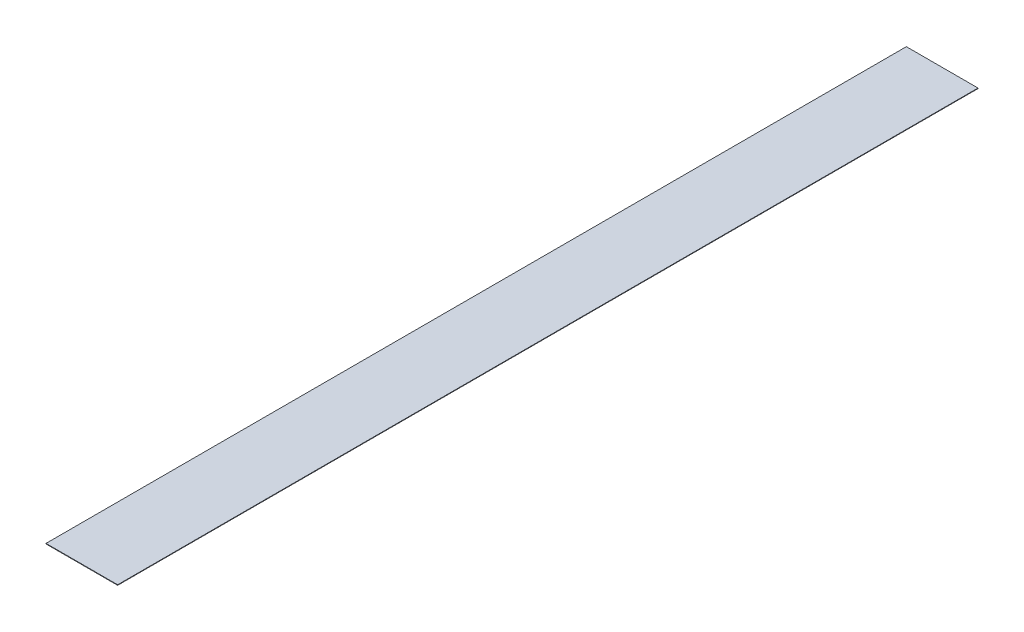
SolidWorks part; units mm, degrees
material "ladder carbon corrected"
ref_plane "Front" through (0, 0, 0) normal (0, 0, 1) x (1, 0, 0)
ref_plane "Top" through (0, 0, 0) normal (0, 1, 0) x (1, 0, 0)
ref_plane "Right" through (0, 0, 0) normal (1, 0, 0) x (0, 0, -1)
sketch "Sketch1" plane through (0, 0, 0) normal (0, 1, 0) x (1, 0, 0)
  line L0 (12.45, 149.5) -> (-12.45, -149.5) construction
  line L1 (-12.45, 149.5) -> (12.45, 149.5)
  line L2 (-12.45, 149.5) -> (-12.45, -149.5)
  line L3 (-12.45, -149.5) -> (12.45, -149.5)
  line L4 (12.45, 149.5) -> (12.45, -149.5)
  point P4 (0, 0)
  dimension "D1" = 299
  dimension "D2" = 24.9
extrude "Extrude1" add sketch "Sketch1" along normal blind 0.175
